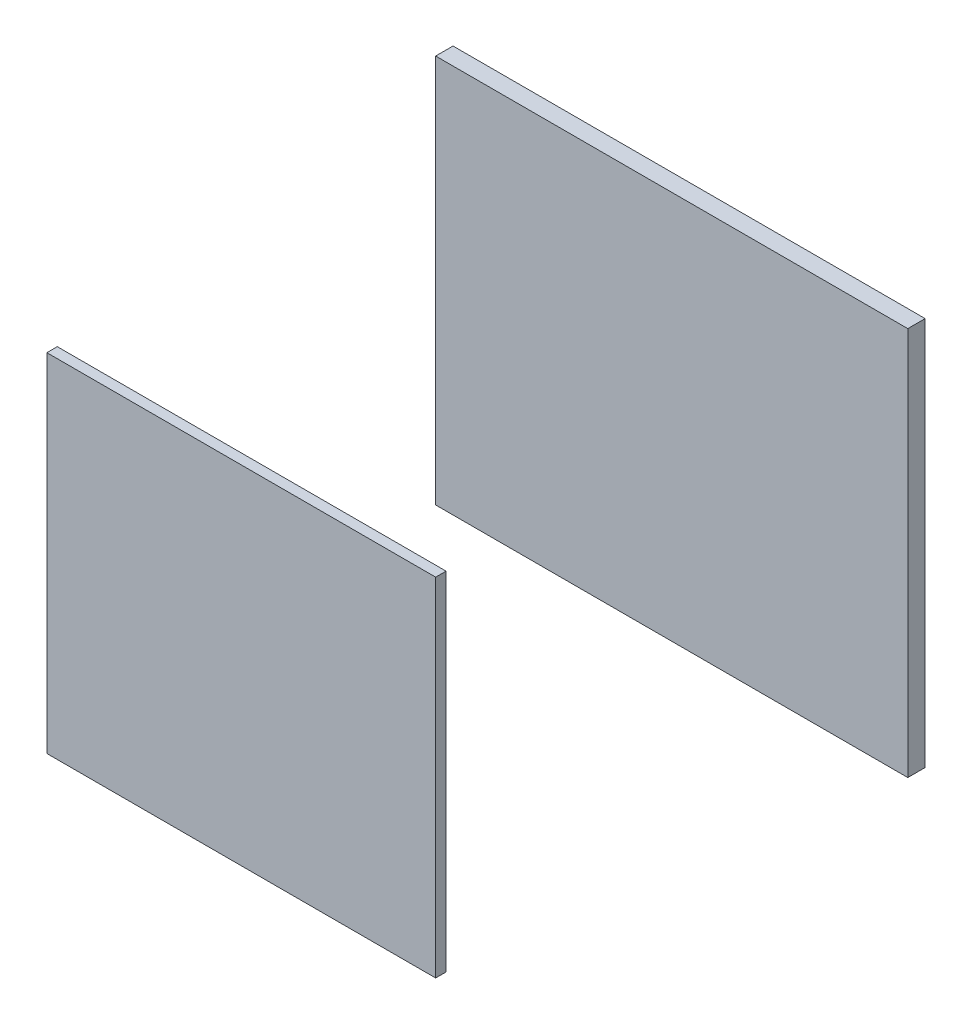
SolidWorks part; units mm, degrees
ref_plane "Front" through (0, 0, 0) normal (0, 0, 1) x (1, 0, 0)
ref_plane "Top" through (0, 0, 0) normal (0, 1, 0) x (1, 0, 0)
ref_plane "Right" through (0, 0, 0) normal (1, 0, 0) x (0, 0, -1)
sketch "Эскиз6" plane through (0, 0, 0) normal (0, 0, 1) x (1, 0, 0)
  line L1 (280, -250) -> (-280, -250)
  line L2 (280, -250) -> (280, 250)
  line L3 (280, 250) -> (-280, 250)
  line L4 (-280, -250) -> (-280, 250)
  line L5 (280, -250) -> (-280, 250) construction
  line L6 (280, 250) -> (-280, -250) construction
  point P0 (0, 0)
  dimension "D1" = 560
  dimension "D2" = 500
extrude "Столик-дерево" add sketch "Эскиз6" against normal blind 15
ref_plane "Плоскость2" through (0, 0, -625) normal (0, 0, 1) x (1, 0, 0)
sketch "Эскиз7" plane through (0, 0, -625) normal (0, 0, 1) x (1, 0, 0)
  line L1 (340, -280) -> (-340, -280)
  line L2 (340, -280) -> (340, 280)
  line L3 (340, 280) -> (-340, 280)
  line L4 (-340, -280) -> (-340, 280)
  line L5 (340, -280) -> (-340, 280) construction
  line L6 (340, 280) -> (-340, -280) construction
  point P0 (0, 0)
  dimension "D1" = 680
  dimension "D2" = 560
extrude "Подставка-металл" add sketch "Эскиз7" along normal blind 5 and the other way blind 20 separate body
